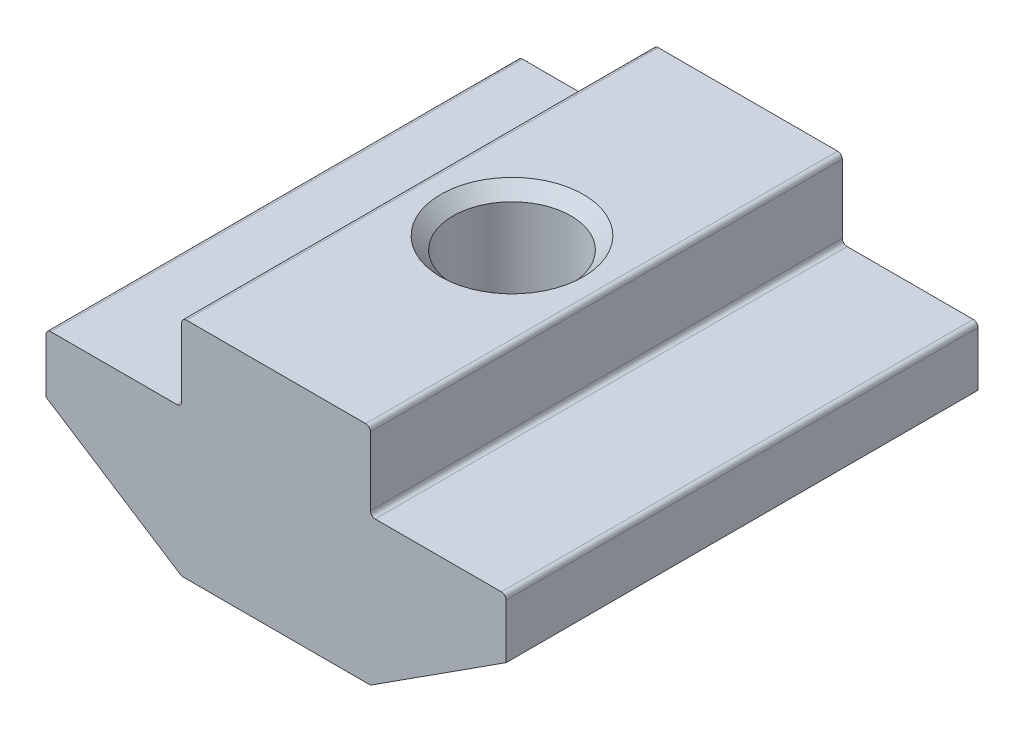
SolidWorks part; units mm, degrees
ref_plane "Спереди" through (0, 0, 0) normal (0, 0, 1) x (1, 0, 0)
ref_plane "Сверху" through (0, 0, 0) normal (0, 1, 0) x (1, 0, 0)
ref_plane "Справа" through (0, 0, 0) normal (1, 0, 0) x (0, 0, -1)
sketch "Эскиз1" plane through (0, 0, 0) normal (0, 0, 1) x (1, 0, 0)
  line L0 (4, 0) -> (-4, 0)
  line L1 (-4, 0) -> (-4, -3.3)
  line L2 (-4, -3.3) -> (-9.75, -3.3)
  line L3 (-9.75, -3.3) -> (-9.75, -5.8)
  line L4 (-9.75, -5.8) -> (-4, -9.5)
  line L5 (-4, -9.5) -> (4, -9.5)
  line L6 (0, -9.5) -> (0, 0) construction
  line L7 (9.75, -5.8) -> (4, -9.5)
  line L8 (9.75, -3.3) -> (9.75, -5.8)
  line L9 (4, -3.3) -> (9.75, -3.3)
  line L10 (4, 0) -> (4, -3.3)
  point P3 (-4, -1.65)
  dimension "D1" = 8
  dimension "D2" = 19.5
  dimension "D3" = 2.5
  dimension "D4" = 9.5
  dimension "D5" = 6.2
extrude "Бобышка-Вытянуть1" add sketch "Эскиз1" along normal mid plane 20
hole_wizard "Отверстие обработанное метчиком M63" positions "Эскиз2" profile "Эскиз4" tap size "M6" standard "ISO" end condition through all
sketch "Эскиз2" plane through (0, 0, 0) normal (0, 1, 0) x (1, 0, 0)
  point P0 (0, 0)
sketch "Эскиз4" plane through (0, 0, 0) normal (1, 0, 0) x (0, 0, 1)
  line L0 (0, 0) -> (0, 9.5)
  line L1 (0, 9.5) -> (3.025, 9.5)
  line L2 (2.5, 8.975) -> (2.5, 0.525)
  line L3 (2.5, 0.525) -> (3.025, 0)
  line L5 (3.025, 0) -> (0, 0)
  line L6 (-2.5, 0.525) -> (-3.025, 0) construction
  line L7 (3.025, 9.5) -> (2.5, 8.975)
  line L8 (-3.025, 9.5) -> (-2.5, 8.975) construction
  line L11 (0, -6.35) -> (0, 107.95) construction
  dimension "Диаметр проходного сверла" = 5
  dimension "Глубина проходного сверла" = 9.5
  dimension "Диаметр передней зенковки" = 6.05
  dimension "Угол передней зенковки" = 90
  dimension "Диаметр задней зенковки" = 6.05
  dimension "Угол задней зенковки" = 90
cosmetic thread "Отверстие резьбы1" parameters "D2"=6
fillet "Скругление1" radius 0.2 8 edges at (4, -9.5, 0) (-4, -9.5, 0) (9.75, -3.3, 0) (4, -3.3, 0) (4, 0, 0) (-4, 0, 0) (-9.75, -3.3, 0) (-4, -3.3, 0)
